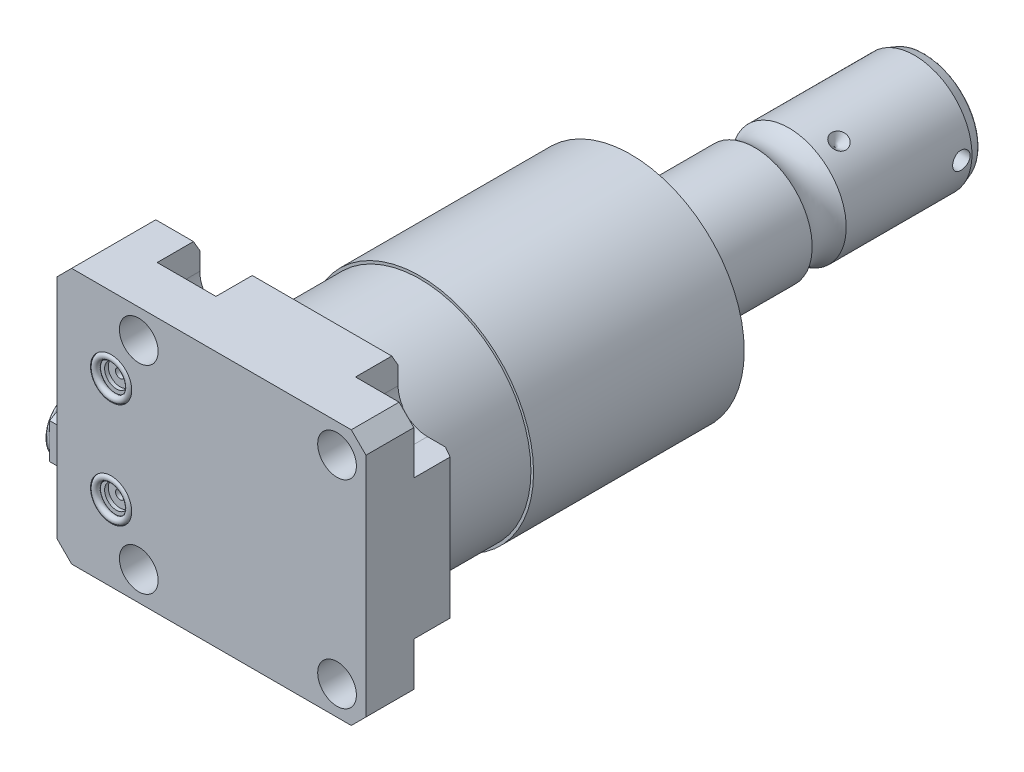
SolidWorks part; units mm, degrees
material "Alloy Steel"
ref_plane "Front Plane" through (0, 0, 0) normal (0, 0, 1) x (1, 0, 0)
ref_plane "Top Plane" through (0, 0, 0) normal (0, 1, 0) x (1, 0, 0)
ref_plane "Right Plane" through (0, 0, 0) normal (1, 0, 0) x (0, 0, -1)
sketch "Sketch1" plane through (0, 0, 0) normal (0, 0, 1) x (1, 0, 0)
  line L0 (-50.063, 35.433) -> (35.433, 35.433)
  line L1 (35.433, 35.433) -> (35.433, -35.433)
  line L2 (35.433, -35.433) -> (-50.063, -35.433)
  line L3 (-50.063, -35.433) -> (-50.063, 35.433)
  dimension "D1" = 85.496
  dimension "D2" = 70.866
  dimension "D3" = 35.433
  dimension "D4" = 35.433
extrude "Extrude1" add sketch "Sketch1" along normal blind 25.019
hole_wizard "Hole1" positions "Sketch22" profile "Sketch21" legacy end condition through all
sketch "Sketch22" plane through (0, 0, 0) normal (0, 0, -1) x (-1, 0, 0)
  line L0 (0, 0) -> (42.7441, 0) construction
  line L1 (0, 0.8532) -> (0, 27.5062) construction
  point P0 (-27.432, -27.432)
  point P9 (-27.432, 27.432)
  point P11 (27.432, 27.432)
  point P12 (27.432, -27.432)
  dimension "D1" = 27.432
  dimension "D2" = 27.432
sketch "Sketch21" plane through (27.432, -27.432, 0) normal (1, 0, 0) x (0, 1, 0)
  line L0 (0, 0) -> (0, 25.019)
  line L1 (0, 25.019) -> (5.3595, 25.019)
  line L2 (5.3595, 25.019) -> (5.3595, 0)
  line L3 (5.3595, 0) -> (0, 0)
  line L4 (0, 110) -> (0, -10) construction
  dimension "Diameter" = 10.719
  dimension "Depth" = 25.019
sketch "Sketch3" plane through (0, 0, 0) normal (0, 0, -1) x (-1, 0, 0)
  line L0 (-27.432, -19.304) -> (-35.433, -19.304)
  line L1 (-35.433, -35.433) -> (-35.433, -19.304)
  line L2 (-35.433, 19.304) -> (-35.433, 35.433)
  line L3 (-35.433, 19.304) -> (-27.432, 19.304)
  line L4 (-19.304, 27.432) -> (-19.304, 35.433)
  line L5 (-35.433, 35.433) -> (-19.304, 35.433)
  line L6 (19.304, 35.433) -> (19.304, 27.432)
  line L7 (35.56, 27.432) -> (35.56, 35.433)
  line L8 (19.304, 35.433) -> (35.56, 35.433)
  line L9 (35.56, -35.433) -> (19.304, -35.433)
  line L10 (35.56, -35.433) -> (35.56, -27.432)
  line L11 (19.304, -27.432) -> (19.304, -35.433)
  line L12 (-19.304, -35.433) -> (-35.433, -35.433)
  line L13 (-19.304, -35.433) -> (-19.304, -27.432)
  line L14 (-35.433, 35.433) -> (50.063, 35.433) construction
  line L15 (-35.433, -35.433) -> (-35.433, 35.433) construction
  line L16 (50.063, -35.433) -> (-35.433, -35.433) construction
  arc A0 (-19.304, -27.432) -> (-27.432, -19.304) centre (-27.432, -27.432) ccw
  arc A1 (-27.432, 19.304) -> (-19.304, 27.432) centre (-27.432, 27.432) ccw
  arc A2 (19.304, 27.432) -> (35.56, 27.432) centre (27.432, 27.432) ccw
  arc A3 (35.56, -27.432) -> (19.304, -27.432) centre (27.432, -27.432) ccw
  circle A8 centre (-27.432, 27.432) radius 5.3595 construction
  circle A9 centre (-27.432, -27.432) radius 5.3595 construction
  circle A10 centre (27.432, -27.432) radius 5.3595 construction
  circle A11 centre (27.432, 27.432) radius 5.3595 construction
  dimension "D1" = 8.128
extrude "Cut-Extrude2" cut sketch "Sketch3" against normal blind 11.786
ref_plane "Plane16" through (0, 0, 12.522) normal (0, 0, 1) x (1, 0, 0)
sketch "Sketch23" plane through (0, 0, 12.522) normal (0, 0, 1) x (1, 0, 0)
  line L0 (-11.9397, -13.0048) -> (-61.0013, -13.0048) construction
  line L1 (-50.063, -23.749) -> (-49.809, -23.749)
  line L3 (-49.809, -23.749) -> (-49.809, -19.6596)
  line L4 (-49.809, -19.6596) -> (-49.0978, -18.9484)
  line L5 (-49.0978, -18.9484) -> (-35.6358, -18.9484)
  line L6 (-35.6358, -18.9484) -> (-35.6358, -13.0048)
  line L7 (-35.6358, -13.0048) -> (-50.063, -13.0048)
  line L8 (-50.063, -13.0048) -> (-50.063, -23.749)
  line L10 (-50.063, 35.433) -> (-50.063, -35.433) construction
  dimension "D1" = 21.4884
  dimension "D2" = 0.254
  dimension "D3" = 45
  dimension "D4" = 13.3096
  dimension "D5" = 11.8872
  dimension "D6" = 14.1732
  dimension "D7" = 13.0048
revolve "Cut-Revolve5" cut sketch "Sketch23" angle 360 about L0
mirror "Mirror1" about plane through (0, 0, 0) normal (0, 1, 0) of "Cut-Revolve5"
sketch "Sketch6" plane through (0, 0, 25.019) normal (0, 0, 1) x (1, 0, 0)
  line L0 (0, 0) -> (-71.0417, 0) construction
  circle A0 centre (-35.077, -14.529) radius 5.7023
  circle A1 centre (-35.077, 14.529) radius 5.7023
  dimension "D4" = 11.4046
  dimension "D1" = 14.529
  dimension "D2" = 29.058
  dimension "D3" = 35.077
extrude "Cut-Extrude3" cut sketch "Sketch6" against normal blind 1.4478
sketch "Sketch7" plane through (0, 0, 23.5712) normal (0, 0, 1) x (1, 0, 0)
  circle A0 centre (-35.077, 14.529) radius 3.2512
  circle A1 centre (-35.077, -14.529) radius 3.2512
  circle A2 centre (-35.077, 14.529) radius 5.7023 construction
  circle A3 centre (-35.077, -14.529) radius 5.7023 construction
  dimension "D1" = 6.5024
extrude "Cut-Extrude4" cut sketch "Sketch7" against normal blind 1.016
sketch "Sketch8" plane through (0, 0, 22.5552) normal (0, 0, 1) x (1, 0, 0)
  circle A0 centre (-35.077, 14.529) radius 1.2446
  circle A1 centre (-35.077, -14.529) radius 1.2446
  circle A2 centre (-35.077, 14.529) radius 5.7023 construction
  circle A3 centre (-35.077, -14.529) radius 5.7023 construction
  dimension "D1" = 2.4892
extrude "Cut-Extrude5" cut sketch "Sketch8" against normal blind 11.9888
ref_plane "Plane17" through (0, 14.5288, 0) normal (0, 1, 0) x (-1, 0, 0)
sketch "Sketch9" plane through (-41.656, 14.5288, 23.5712) normal (0, 1, 0) x (1, 0, 0)
  line L0 (6.579, -1.9469) -> (6.579, 0.0927) construction
  line L3 (0.8767, 0) -> (12.2813, 0) construction
  line L4 (6.579, 13.0048) -> (6.579, 1.016) construction
  circle A0 centre (11.3542, -0.9271) radius 0.9271
  dimension "D1" = 1.8542
  dimension "D2" = 9.5504
revolve "Revolve1" add sketch "Sketch9" angle 360 about L0
mirror "Mirror2" about plane through (0, 0, 0) normal (0, 1, 0) of bodies 116
chamfer "Chamfer1" distance 4.064 angle 45 4 edges at (35.433, -35.433, 18.4025) (35.433, 35.433, 18.4025) (-50.063, 35.433, 12.5095) (-50.063, -35.433, 12.5095)
chamfer "Chamfer2" distance 3.0226 angle 30 5 edges at (-40.7795, -35.433, 0) (0, -35.433, 0) (35.433, 0, 0) (-40.7795, 35.433, 0) (0, 35.433, 0)
sketch "Sketch24" plane through (0, 0, 0) normal (1, 0, 0) x (0, 0, -1)
  line L0 (0, 0) -> (113.9127, 0) construction
  line L1 (0, 0) -> (0, 30.658)
  line L2 (0, 30.658) -> (25.4, 30.658)
  line L3 (25.4, 30.658) -> (25.4, 31.3945)
  line L4 (25.4, 31.3945) -> (83.6873, 31.3945)
  line L5 (83.6873, 31.3945) -> (86.995, 19.05)
  line L6 (86.995, 19.05) -> (86.995, 0)
  line L7 (86.995, 0) -> (0, 0)
  dimension "D1" = 61.316
  dimension "D2" = 25.4
  dimension "D3" = 62.789
  dimension "D4" = 38.1
  dimension "D5" = 15
  dimension "D6" = 86.995
revolve "Revolve4" add sketch "Sketch24" angle 360 about L0
sketch "Sketch17" plane through (0, 0, 0) normal (1, 0, 0) x (0, 0, -1)
  line L0 (86.995, 0) -> (86.995, -15.875)
  line L1 (86.995, -15.875) -> (118.0007, -15.875)
  line L2 (127.4153, -15.875) -> (162.205, -15.875)
  line L3 (165.126, -14.8118) -> (165.126, 0)
  line L4 (165.126, 0) -> (86.995, 0)
  line L5 (130.8989, 0) -> (0.816, 0) construction
  line L6 (86.995, -19.05) -> (86.995, 19.05) construction
  line L7 (-25.019, -31.369) -> (-25.019, 31.369) construction
  line L8 (165.126, -14.8118) -> (162.205, -15.875)
  arc A0 (127.4153, -15.875) -> (118.0007, -15.875) centre (122.708, -22.2505) ccw
  dimension "D2" = 20
  dimension "D4" = 7.925
  dimension "D5" = 28.651
  dimension "D1" = 190.145
  dimension "D3" = 31.75
  dimension "D6" = 42.418
  dimension "D7" = 2.921
revolve "Revolve3" add sketch "Sketch17" angle 360 about L5
sketch "Sketch26" plane through (-49.809, 0, 0) normal (-1, 0, 0) x (0, 0, 1)
  circle A0 centre (12.522, -13.0048) radius 8.509
  dimension "D1" = 17.018
extrude "Extrude2" add sketch "Sketch26" along normal blind 7.874
fillet "Fillet1" radius 1.016 1 edges at (-57.683, -21.5138, 12.522)
sketch "Sketch27" plane through (-57.683, 0, 0) normal (-1, 0, 0) x (0, 0, 1)
  line L1 (4.013, -8.0921) -> (4.013, -17.9175)
  line L2 (4.013, -17.9175) -> (12.522, -22.8301)
  line L3 (12.522, -22.8301) -> (21.031, -17.9175)
  line L4 (21.031, -17.9175) -> (21.031, -8.0921)
  line L5 (21.031, -8.0921) -> (12.522, -3.1795)
  line L6 (12.522, -3.1795) -> (4.013, -8.0921)
  circle A0 centre (12.522, -13.0048) radius 8.509 construction
  dimension "D1" = 17.018
extrude "Extrude3" add sketch "Sketch27" against normal blind 5.0038 from offset 1.6002 offset against normal yes
sketch "Sketch28" plane through (0, 0, -165.126) normal (0, 0, -1) x (-1, 0, 0)
  circle A0 centre (0, 0) radius 12.827
  circle A1 centre (0, 0) radius 12.573
  dimension "D1" = 25.654
  dimension "D2" = 25.146
extrude "Cut-Extrude6" cut sketch "Sketch28" against normal blind 0.3
sketch "Sketch29" plane through (0, 0, -165.126) normal (0, 0, -1) x (-1, 0, 0)
  line L1 (4, -2.3094) -> (4, 2.3094)
  line L2 (4, 2.3094) -> (0, 4.6188)
  line L3 (0, 4.6188) -> (-4, 2.3094)
  line L4 (-4, 2.3094) -> (-4, -2.3094)
  line L5 (-4, -2.3094) -> (0, -4.6188)
  line L6 (0, -4.6188) -> (4, -2.3094)
  circle A0 centre (0, 0) radius 4 construction
  dimension "D1" = 8
extrude "Cut-Extrude7" cut sketch "Sketch29" against normal blind 8
sketch "Sketch30" plane through (0, 0, 0) normal (0, 1, 0) x (1, 0, 0)
  line L0 (-27.8193, 133.376) -> (0.6125, 133.376) construction
  line L1 (-15.875, 135.789) -> (-13.462, 133.376)
  line L2 (-15.875, 162.205) -> (-15.875, 127.4153) construction
  line L3 (-13.462, 133.376) -> (-15.875, 133.376)
  line L4 (-15.875, 133.376) -> (-15.875, 135.789)
  arc A0 (-15.875, 118.0007) -> (-15.875, 127.4153) centre (-22.2505, 122.708) ccw construction
  dimension "D1" = 45
  dimension "D2" = 4.826
  dimension "D3" = 10.668
revolve "Cut-Revolve6" cut sketch "Sketch30" angle 360 about L0
pattern_circular "CirPattern1" count 3 over 360 about axis through (0, 0, -130.8989) along (0, 0, -1) of "Cut-Revolve6"
sketch "Sketch31" plane through (0, 0, 0) normal (0, 1, 0) x (1, 0, 0)
  line L0 (-9.1879, 159.284) -> (41.8961, 159.284) construction
  line L1 (15.875, 127.4153) -> (15.875, 162.205) construction
  line L2 (15.875, 161.697) -> (12.065, 161.697)
  line L3 (15.875, 161.697) -> (15.875, 159.284)
  line L4 (15.875, 159.284) -> (12.065, 159.284)
  line L5 (12.065, 161.697) -> (12.065, 159.284)
  line L6 (12.573, 165.126) -> (-12.573, 165.126) construction
  dimension "D1" = 5.842
  dimension "D2" = 4.826
  dimension "D3" = 3.81
revolve "Cut-Revolve7" cut sketch "Sketch31" angle 360 about L0
fillet "Fillet2" radius 0.635 1 edges at (-14.8118, 0, -165.126)
